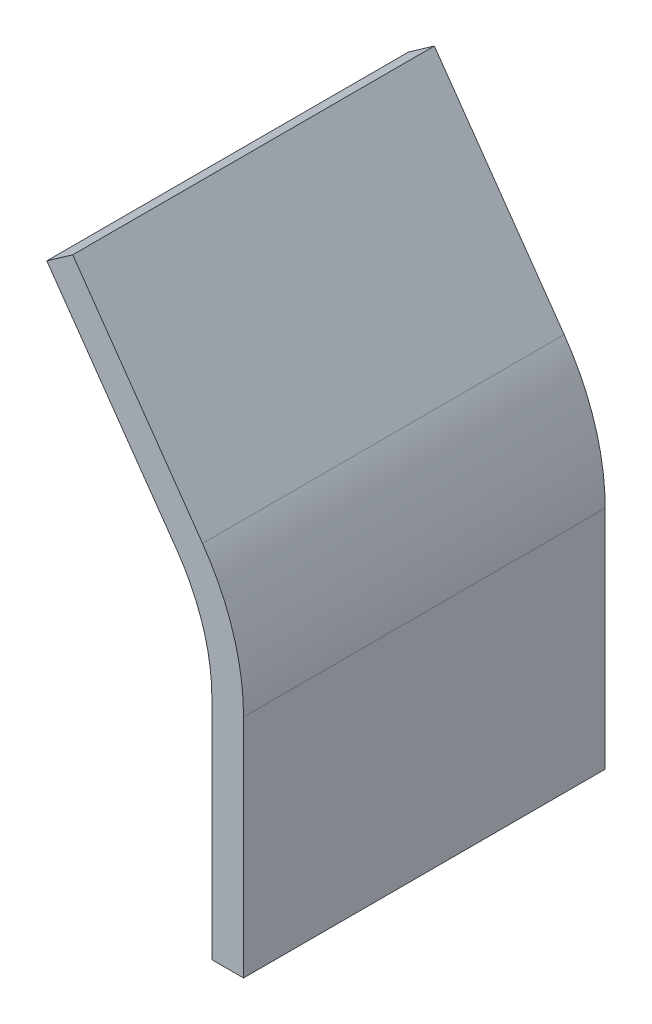
SolidWorks part; units mm, degrees
ref_plane "Alzado" through (0, 0, 0) normal (0, 0, 1) x (1, 0, 0)
ref_plane "Planta" through (0, 0, 0) normal (0, 1, 0) x (1, 0, 0)
ref_plane "Vista lateral" through (0, 0, 0) normal (1, 0, 0) x (0, 0, -1)
sketch "Croquis1" plane through (0, 0, 0) normal (0, 0, 1) x (1, 0, 0)
  line L0 (-18.8971, 59.8246) -> (-4.5362, 39.3608)
  line L1 (0, 25) -> (0, 0)
  arc A0 (-4.5362, 39.3608) -> (0, 25) centre (-25, 25) cw
  point P5 (0, 0)
  point P6 (0, 0)
  point P7 (0, 0)
  dimension "D1" = 25
  dimension "D2" = 25
  dimension "D3" = 25
  dimension "D4" = 144.94
extrude "Extruir-Lámina1" add sketch "Croquis1" along normal mid plane 40 thin
